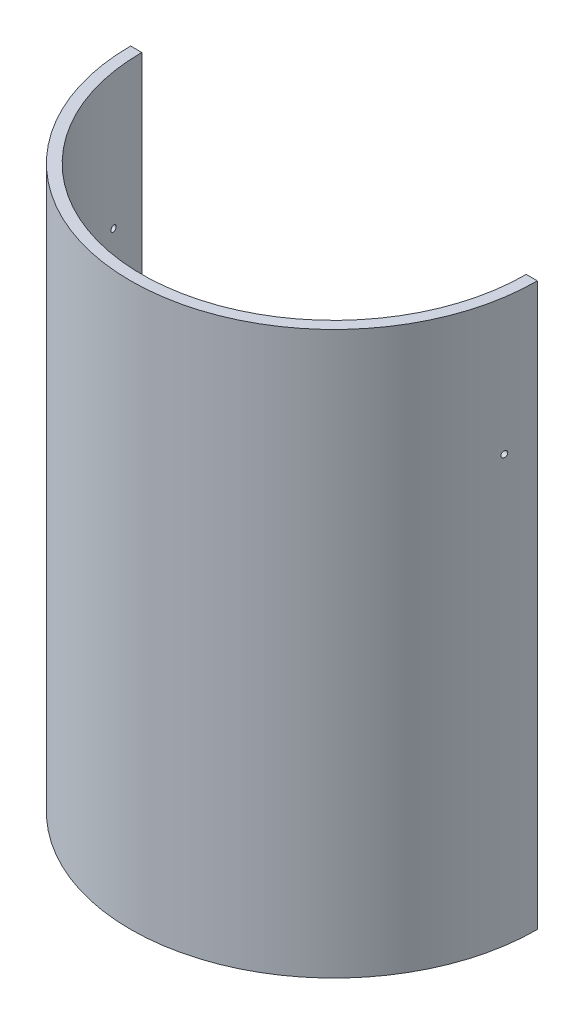
SolidWorks part; units mm, degrees
material "PET"
ref_plane "Front Plane" through (0, 0, 0) normal (0, 0, 1) x (1, 0, 0)
ref_plane "Top Plane" through (0, 0, 0) normal (0, 1, 0) x (1, 0, 0)
ref_plane "Right Plane" through (0, 0, 0) normal (1, 0, 0) x (0, 0, -1)
sketch "Sketch1" plane through (0, 0, 0) normal (0, 1, 0) x (1, 0, 0)
  circle A0 centre (0, 0) radius 94.996
  circle A1 centre (0, 0) radius 53.975
  dimension "D1" = 189.992
  dimension "D2" = 107.95
extrude "Top of Hatch" add sketch "Sketch1" along normal blind 3.302
sketch "Sketch2" plane through (0, 3.302, 0) normal (0, 1, 0) x (1, 0, 0)
  circle A0 centre (0, 0) radius 94.996
  circle A1 centre (0, 0) radius 89.789
  circle A2 centre (0, 0) radius 94.996 construction
  dimension "D1" = 179.578
extrude "Hatch Body" add sketch "Sketch2" along normal blind 259.08
sketch "Sketch3" plane through (0, 0, 0) normal (0, -1, 0) x (1, 0, 0)
  line L0 (0, 0) -> (-76.454, 0) construction
  line L1 (0, 0) -> (0, 76.902) construction
  circle A0 centre (-76.454, 0) radius 13.335
  circle A1 centre (76.454, 0) radius 13.335
  dimension "D1" = 76.454
  dimension "D2" = 26.67
extrude "Charge Tube Holes" cut sketch "Sketch3" against normal through all
sketch "Sketch4" plane through (0, 0, 0) normal (0, -1, 0) x (1, 0, 0)
  line L0 (0, 0) -> (94.996, 0) construction
  line L1 (0, 0) -> (-38.1, -65.9911) construction
  circle A2 centre (-38.1, -65.9911) radius 3.81
  circle A4 centre (0, 0) radius 94.996 construction
  circle A5 centre (-76.2, 0) radius 3.81 [skipped]
  circle A6 centre (-38.1, 65.9911) radius 3.81
  circle A7 centre (38.1, 65.9911) radius 3.81
  circle A8 centre (76.2, 0) radius 3.81 [skipped]
  circle A9 centre (38.1, -65.9911) radius 3.81
  dimension "D1" = 6
  dimension "D9" = 7.62
  dimension "D2" = 76.2
  dimension "D8" = 38.1
extrude "Bolt Holes" cut sketch "Sketch4" against normal through all
sketch "Sketch 5" plane through (0, 0, 0) normal (0, -1, 0) x (1, 0, 0)
  circle A0 centre (-26.1124, 57.3248) radius 5.08
  circle A1 centre (9.1936, 61.0335) radius 5.08
  dimension "D1" = 10.16
  dimension "D2" = 10.16
  dimension "D3" = 62.992
  dimension "D4" = 61.722
  dimension "D5" = 26.1124
  dimension "D6" = 35.306
extrude "Antenna Holes " cut sketch "Sketch 5" against normal through all
sketch "Sketch5" plane through (0, 0, 0) normal (0, -1, 0) x (1, 0, 0)
  line L0 (0, -104.4956) -> (0, 104.4956) construction
  line L2 (104.4956, 0) -> (-104.4956, 0) construction
  circle A0 centre (58.42, 0) radius 3.81
  circle A1 centre (-58.42, 0) radius 3.81
  circle A3 centre (39.878, 41.91) radius 3.175
  circle A4 centre (-39.878, 41.91) radius 3.175
  circle A5 centre (39.878, -41.91) radius 3.175
  circle A6 centre (-39.878, -41.91) radius 3.175
  dimension "D1" = 7.62
  dimension "D3" = 6.35
  dimension "D2" = 58.42
  dimension "D4" = 41.91
  dimension "D5" = 39.878
extrude "Inner Screw Holes" cut sketch "Sketch5" against normal through all
sketch3d "3DSketch3" plane through (0, 0, 0) normal (0, 0, 1) x (1, 0, 0)
  dimension "D1" = 94.996
sketch "Sketch8" plane through (94.996, 0, 0) normal (1, 0, 0) x (0, 0, -1)
  line L0 (0, 0) -> (0, 262.382) construction
  line L1 (94.996, 262.382) -> (-94.996, 262.382) construction
  line L2 (0, 198.882) -> (50000, 198.882) construction
  circle A0 centre (0, 198.882) radius 1.4351 construction
  circle A1 centre (14.351, 198.882) radius 1.397
  circle A2 centre (-14.351, 198.882) radius 1.397
  dimension "D1" = 2.8702
  dimension "D3" = 2.794
  dimension "D2" = 63.5
  dimension "D4" = 14.351
extrude "Cut-Extrude1" cut sketch "Sketch8" against normal through all
sketch "Sketch12" plane through (0, 0, 0) normal (0, -1, 0) x (1, 0, 0)
  line L0 (-94.996, 0) -> (94.996, 0)
  circle A0 centre (0, 0) radius 94.996 construction
  arc A1 (-94.996, 0) -> (94.996, 0) centre (0, 0) ccw
extrude "Cut-Extrude4" cut sketch "Sketch12" against normal through all
